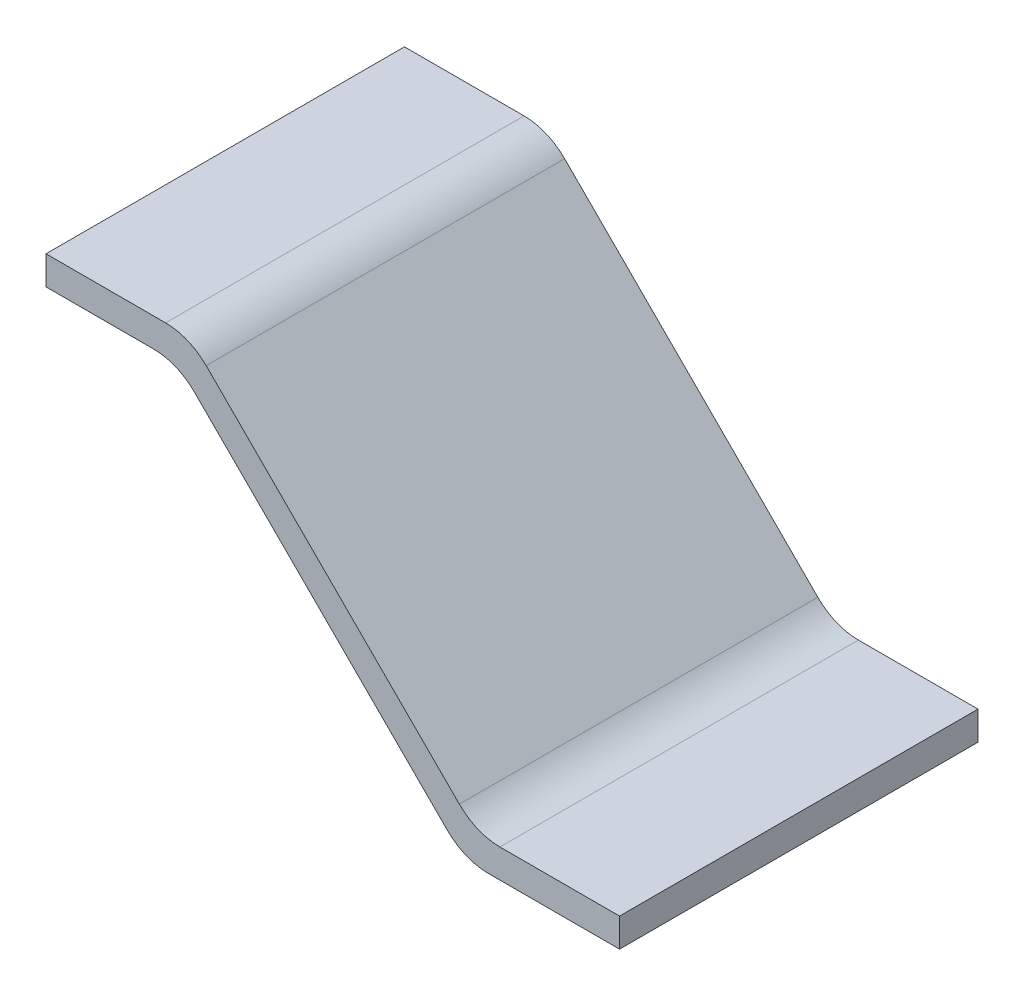
SolidWorks part; units mm, degrees
ref_plane "Front Plane" through (0, 0, 0) normal (0, 0, 1) x (1, 0, 0)
ref_plane "Top Plane" through (0, 0, 0) normal (0, 1, 0) x (1, 0, 0)
ref_plane "Right Plane" through (0, 0, 0) normal (1, 0, 0) x (0, 0, -1)
sketch "Sketch4" plane through (0, 0, 0) normal (0, 0, 1) x (1, 0, 0)
  line L0 (0, 0) -> (0.5, 0)
  line L1 (0.5, 0) -> (1.5, -1)
  line L2 (1.5, -1) -> (2, -1)
  line L3 (0, -0.1) -> (0.4586, -0.1)
  line L4 (0.4586, -0.1) -> (1.4586, -1.1)
  line L5 (1.4586, -1.1) -> (2, -1.1)
  line L6 (0, -0.1) -> (0, 0)
  line L7 (2, -1.1) -> (2, -1)
  dimension "D1" = 1
  dimension "D2" = 0.5
  dimension "D3" = 0.5
  dimension "D4" = 1
  dimension "D5" = 0.1
extrude "Boss-Extrude1" add sketch "Sketch4" along normal mid plane 1.25
fillet "Fillet4" radius 0.2 4 edges at (0.4586, -0.1, 0) (1.4586, -1.1, 0) (1.5, -1, 0) (0.5, 0, 0)
